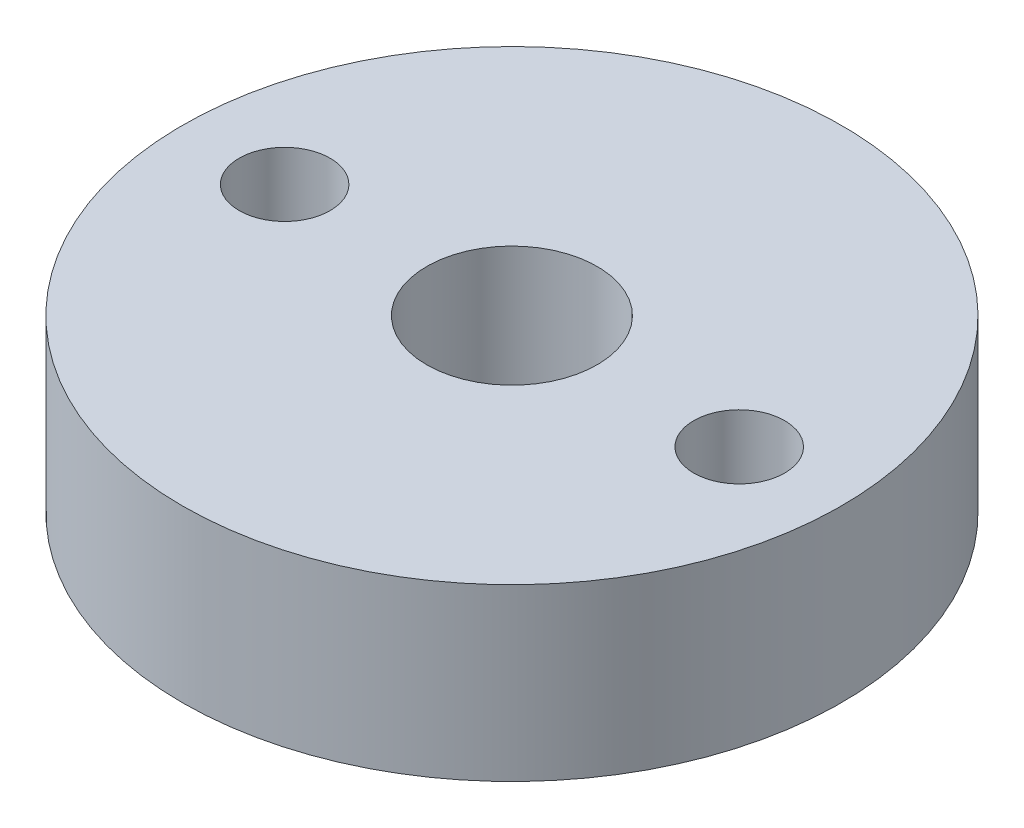
SolidWorks part; units mm, degrees
material "MDF"
ref_plane "Plano frontal" through (0, 0, 0) normal (0, 0, 1) x (1, 0, 0)
ref_plane "Plano superior" through (0, 0, 0) normal (0, 1, 0) x (1, 0, 0)
ref_plane "Plano direito" through (0, 0, 0) normal (1, 0, 0) x (0, 0, -1)
ref_plane "Plano1" through (0, -6, 0) normal (0, -1, 0) x (1, 0, 0)
sketch "Esboço1" plane through (0, -6, 0) normal (0, -1, 0) x (1, 0, 0)
  line L0 (-8, 0) -> (8, 0) construction
  circle A0 centre (8, 0) radius 1.6
  circle A1 centre (0, 0) radius 3
  circle A2 centre (-8, 0) radius 1.6
  circle A3 centre (0, 0) radius 11.6
  dimension "D1" = 23.2
  dimension "D2" = 3.2
  dimension "D3" = 6
  dimension "D4" = 16
extrude "Ressalto-extrusão1" add sketch "Esboço1" against normal blind 6
